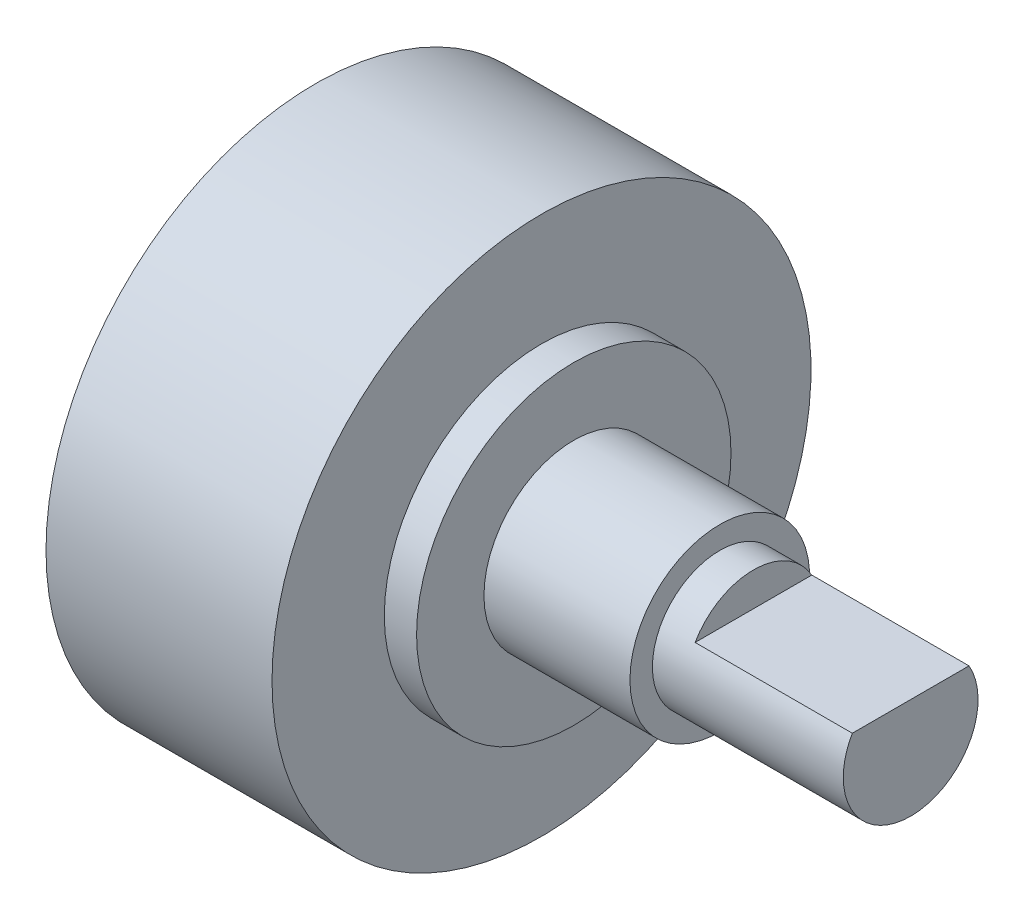
SolidWorks part; units mm, degrees
ref_plane "Front Plane" through (0, 0, 0) normal (0, 0, 1) x (1, 0, 0)
ref_plane "Top Plane" through (0, 0, 0) normal (0, 1, 0) x (1, 0, 0)
ref_plane "Right Plane" through (0, 0, 0) normal (1, 0, 0) x (0, 0, -1)
sketch "Sketch1" plane through (0, 0, 0) normal (0, 0, 1) x (1, 0, 0)
  line L0 (0, 0) -> (26.5, 0)
  line L1 (26.5, 0) -> (26.5, 3)
  line L2 (26.5, 3) -> (18, 3)
  line L3 (18, 3) -> (18, 4)
  line L4 (18, 4) -> (11.5, 4)
  line L5 (11.5, 4) -> (11.5, 7)
  line L6 (11.5, 7) -> (10.0631, 7)
  line L7 (10.0631, 7) -> (10.0631, 12)
  line L8 (10.0631, 12) -> (0, 12)
  line L9 (0, 12) -> (0, 0)
  dimension "D1" = 11.5
  dimension "D2" = 15
  dimension "D3" = 6.5
  dimension "D4" = 12
  dimension "D5" = 3
  dimension "D6" = 4
  dimension "D7" = 7
revolve "Revolve1" add sketch "Sketch1" angle 360 about L0
sketch "Sketch2" plane through (26.5, 0, 0) normal (1, 0, 0) x (0, 0, -1)
  line L0 (-2.5981, 1.5) -> (2.5981, 1.5)
  circle A0 centre (0, 0) radius 3 construction
  arc A1 (-2.5981, 1.5) -> (2.5981, 1.5) centre (0, 0) cw
  dimension "D1" = 1.5
extrude "Cut-Extrude1" cut sketch "Sketch2" against normal blind 7
